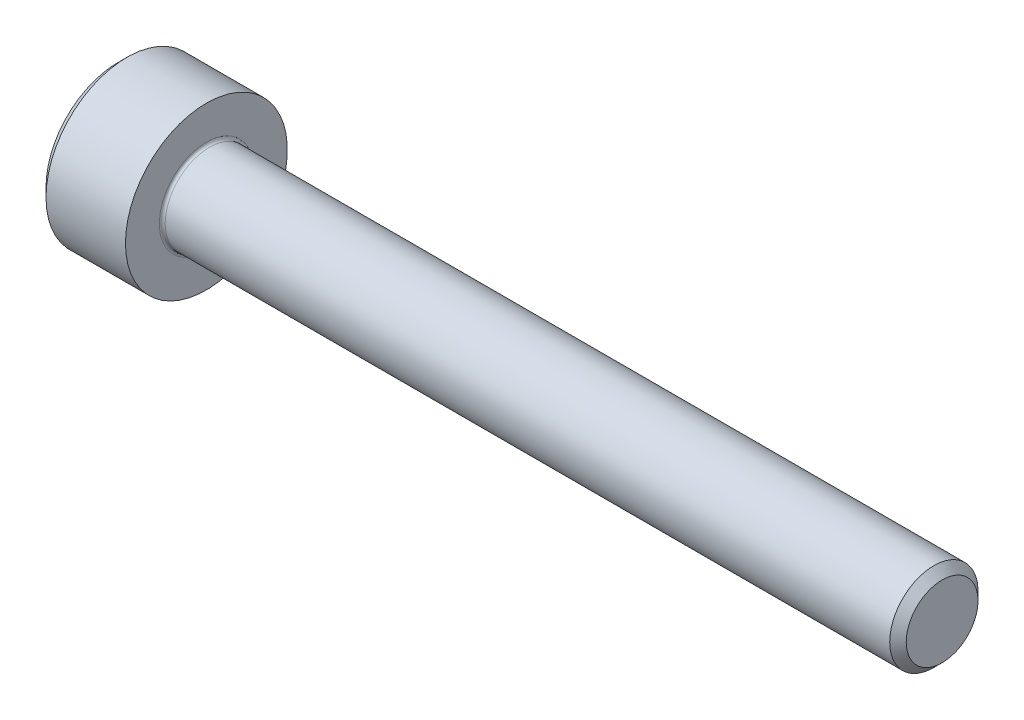
SolidWorks part; units mm, degrees
revolve "Base-Revolve" add sketch "BodySke"
sketch "BodySke" plane through (0, 0, 0) normal (0, 0, 1) x (1, 0, 0)
  line L0 (0, 0) -> (0, 2.45)
  line L1 (0.3, 2.75) -> (3, 2.75)
  line L2 (3, 2.75) -> (3, 1.5)
  line L3 (3, 1.5) -> (27.7195, 1.5)
  line L4 (28, 1.2195) -> (28, 0)
  line L5 (28, 0) -> (0, 0)
  line L6 (-31.75, 0) -> (127, 0) construction
  line L7 (0, 2.45) -> (0.3, 2.75)
  line L8 (28, 1.2195) -> (27.7195, 1.5)
  line L9 (0, -2.45) -> (0.3, -2.75) construction
  line L10 (28, -1.2195) -> (27.7195, -1.5) construction
  line L11 (3.5, 9.525) -> (3.5, 3.175) construction
  line L12 (10, 9.525) -> (10, 3.175) construction
  line L13 (-22, 9.525) -> (-22, 3.175) construction
  dimension "Diameter" = 3
  dimension "Head_ht" = 3
  dimension "Length" = 25
  dimension "Body_ch_ang" = 45
  dimension "Head_dia" = 5.5
  dimension "Head_ch_ang" = 45
  dimension "Minor_dia" = 2.439
  dimension "Advance" = 0.5
  dimension "Thread_nom" = 18
  dimension "Thread_length" = 50
  dimension "Head_ch_ht" = 0.3
cosmetic thread "ThreadCosmetic"
fillet "Fillet1" radius 0.1 1 edges at (3, 0, 1.5)
ref_plane "Plane1" through (0, 0, 0) normal (0, 0, 1) x (1, 0, 0)
ref_plane "Plane2" through (0, 0, 0) normal (0, 1, 0) x (1, 0, 0)
ref_plane "Plane3" through (0, 0, 0) normal (1, 0, 0) x (0, 0, -1)
sketch "Sketch2" plane through (0, 0, 0) normal (0, 0, 1) x (1, 0, 0)
  line L0 (0, 1.28) -> (1.3, 1.28)
  line L1 (1.3, 1.28) -> (2.039, 0)
  line L2 (-31.75, 0) -> (127, 0) construction
  line L3 (2.039, 0) -> (0, 0)
  line L4 (0, 0) -> (0, 1.28)
  line L5 (0, 2.45) -> (0, -2.45) construction
  line L6 (0, 0) -> (47.625, 0) construction
  line L7 (3, -2.75) -> (3, 2.75) construction
  dimension "D1" = 1.28
  dimension "D2" = 60
revolve "Hex-PreBroach" cut sketch "Sketch2" angle 360 about L6
sketch "Sketch3" plane through (0, 0, 0) normal (-1, 0, 0) x (0, 0.5, 0.866)
  line L0 (0.739, 1.28) -> (-0.739, 1.28)
  line L1 (-0.739, 1.28) -> (-1.478, 0)
  line L2 (0.739, 1.28) -> (1.478, 0)
  line L3 (0.739, -1.28) -> (1.478, 0)
  line L4 (0.739, -1.28) -> (-0.739, -1.28)
  line L5 (-0.739, -1.28) -> (-1.478, 0)
  dimension "D1" = 1.28
  dimension "D2" = 1.28
  dimension "Hex_size" = 2.56
extrude "Hex" cut sketch "Sketch3" against normal blind 1.3
sketch "Sketch4" plane through (0, 0, 0) normal (-1, 0, 0) x (0, 0, 1)
  line L0 (0, 0) -> (1.4605, 0)
  line L1 (0, 0) -> (6.1484, 3.5498) construction
  line L2 (0, 0) -> (0.7302, 1.2648)
  line L3 (1.2009, 0.3267) -> (1.3933, 0.4378)
  line L4 (0.8834, 0.8767) -> (1.0758, 0.9877)
  arc A0 (1.2009, 0.3267) -> (0.8834, 0.8767) centre (0, 0) ccw
  arc A1 (1.4605, 0) -> (1.3933, 0.4378) centre (0, 0) ccw
  arc A2 (0.7302, 1.2648) -> (1.0758, 0.9877) centre (0, 0) cw
  dimension "D1" = 30
  dimension "D2" = 60
  dimension "Spline_p_dim" = 0.635
  dimension "D3" = 0.3175
extrude "Spline" [suppressed] cut sketch "Sketch4" against normal blind 1.3
pattern_circular "CirPattern1" [suppressed] count 6 every 60
sketch "Sketch5" plane through (0, 0, 0) normal (0, 0, 1) x (1, 0, 0)
  line L0 (-31.75, 0) -> (127, 0) construction
  line L2 (0, 2.45) -> (0, -2.45) construction
  circle A0 centre (1.2, 0) radius 0.475
  dimension "Drilled_hole_dia" = 0.95
  dimension "Drilled_hole_loc" = 1.2
extrude "Hole" [suppressed] cut sketch "Sketch5" against normal through all and the other way through all
pattern_circular "Drilled-4" [suppressed] count 2 every 60
pattern_circular "Drilled-6" [suppressed] count 3 every 60
sketch "ThdSchSke" plane through (0, 0, 0) normal (0, 0, 1) x (1, 0, 0)
  line L0 (10, -1.2195) -> (9.8036, -1.5)
  line L1 (10, -1.2195) -> (10.1964, -1.5)
  line L2 (10.1964, -1.5) -> (10.1964, -1.875)
  line L3 (-3.175, 0) -> (5.1513, 0) construction
  line L5 (10.1964, -1.875) -> (9.8036, -1.875)
  line L6 (9.8036, -1.875) -> (9.8036, -1.5)
  line L7 (0, 2.45) -> (0, -2.45) construction
  dimension "Thread_minor" = 2.439
  dimension "Diameter" = 3
  dimension "Start" = 10
revolve "ThreadSchematic" [suppressed] cut sketch "ThdSchSke" angle 360 about L3
pattern_linear "ThdSchPat" [suppressed]
equation "\"D2@Sketch3\" = \"Hex_size@Sketch3\" / 2"
equation "\"D1@Sketch3\" = \"Hex_size@Sketch3\" / 2"
equation "\"D1@Sketch2\" = \"Hex_size@Sketch3\" / 2"
equation "\"D3@Sketch4\" = \"Spline_p_dim@Sketch4\" / 2"
equation "\"Thread_minor@ThreadCosmetic\"  =  \"Minor_dia@BodySke\""
equation "\"D2@CirPattern1\" = 360 / \"Num_teeth@CirPattern1\""
equation "\"Wall_thickness@Sketch2\" = \"Head_ht@BodySke\" - \"Key_eng@Hex\""
equation "\"Thread_length@ThreadCosmetic\" = ((sgn( (\"Length@BodySke\" - \"Advance@BodySke\" ) - \"Thread_nom@BodySke\" )-1)*( (\"Length@BodySke\" - \"Advance@BodySke\" ) - \"Thread_nom@BodySke\" ))/-2+ \"Thread_nom@BodySke\""
equation "\"Thread_minor@ThdSchSke\" = \"Minor_dia@BodySke\""
equation "\"Diameter@ThdSchSke\" = \"Diameter@BodySke\""
equation "\"Overcut@ThdSchSke\" = \"Diameter@BodySke\" * 1.25"
equation "\"Start@ThdSchSke\" = \"Head_ht@BodySke\" + \"Length@BodySke\" - \"Thread_length@ThreadCosmetic\"  '---Non-countersunk---"
equation "\"Num_threads@ThdSchPat\" = int( \"Thread_length@ThreadCosmetic\" / \"Advance@BodySke\" + 0.999 )  + 1"
equation "\"Advance@ThdSchPat\" = \"Thread_length@ThreadCosmetic\" /  (\"Num_threads@ThdSchPat\" - 1) 'relax it"
equation "\"Num_threads@ThdSchPat\" = \"Num_threads@ThdSchPat\" - sgn( \"Num_threads@ThdSchPat\" - 1) '---chamfered tips only---"
